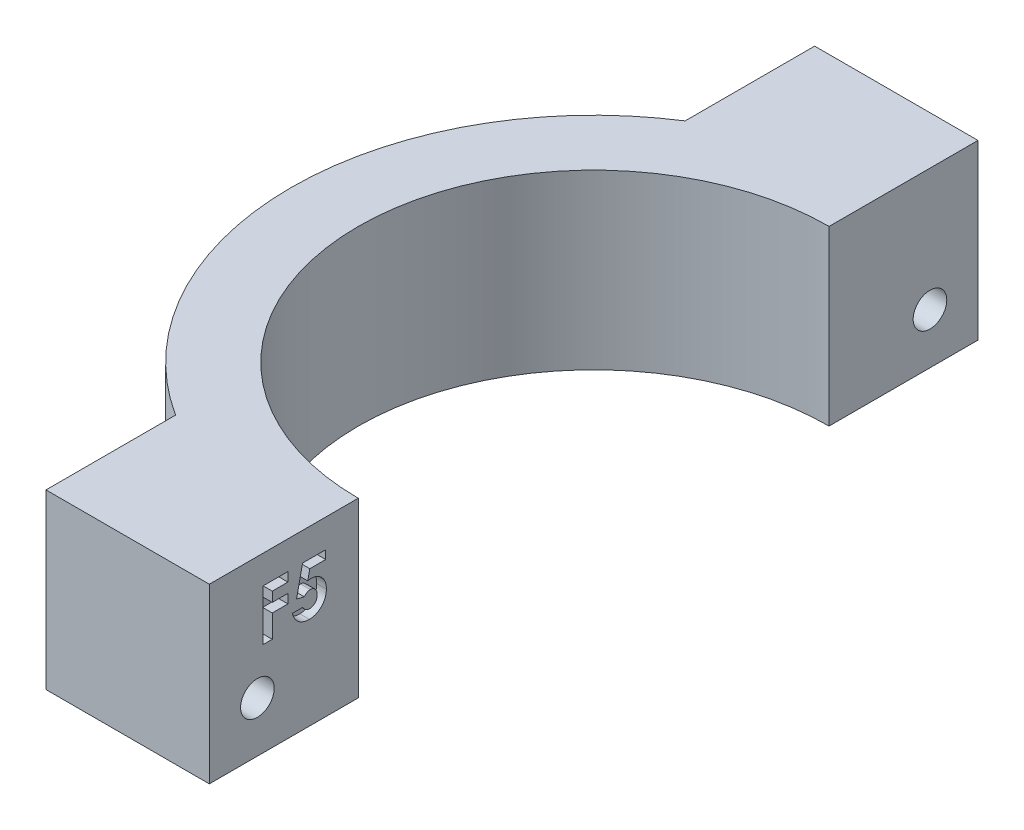
SolidWorks part; units mm, degrees
ref_plane "Front Plane" through (0, 0, 0) normal (0, 0, 1) x (1, 0, 0)
ref_plane "Top Plane" through (0, 0, 0) normal (0, 1, 0) x (1, 0, 0)
ref_plane "Right Plane" through (0, 0, 0) normal (1, 0, 0) x (0, 0, -1)
sketch "Sketch1" plane through (0, 0, 0) normal (0, 1, 0) x (1, 0, 0)
  line L0 (-46.9983, 32.5286) -> (-46.9983, -47.4714)
  line L1 (-46.9983, -47.4714) -> (-12.9983, -47.4714)
  line L2 (-12.9983, -47.4714) -> (-12.9983, -31.9714)
  line L3 (-46.9983, 32.5286) -> (-12.9983, 32.5286)
  line L4 (-12.9983, 32.5286) -> (-12.9983, 17.0286)
  line L5 (-29.9983, 32.5286) -> (-29.9983, 19.0474)
  line L6 (-29.9983, -47.4714) -> (-29.9983, -33.9903)
  arc A0 (-12.9983, 17.0286) -> (-12.9983, -31.9714) centre (-12.9983, -7.4714) ccw
  arc A1 (-12.9983, 24.0286) -> (-12.9983, -38.9714) centre (-12.9983, -7.4714) ccw
  dimension "D1" = 80
  dimension "D2" = 34
  dimension "D3" = 34
  dimension "D4" = 15.5
  dimension "D5" = 15.5
  dimension "D6" = 49
  dimension "D7" = 7
extrude "Boss-Extrude1" add sketch "Sketch1" along normal blind 18 contours A1 L4 L3 L5 | L4 A1 L2 A0 | A1 L6 L1 L2
sketch "Sketch2" plane through (-12.9983, 0, 0) normal (1, 0, 0) x (0, 0, -1)
  line L0 (-47.4714, 18) -> (-47.4714, 0) construction
  line L3 (32.5286, 18) -> (32.5286, 0) construction
  line L8 (-47.4714, 18) -> (-31.9714, 18) construction
  line L9 (32.5286, 18) -> (17.0286, 18) construction
  circle A0 centre (-42.4714, 5.25) radius 1.75
  circle A1 centre (27.5286, 5.25) radius 1.75
  dimension "D3" = 12.75
  dimension "D5" = 3.5
  dimension "D6" = 3.5
  dimension "D1" = 5
  dimension "D2" = 5
  dimension "D4" = 12.75
extrude "Cut-Extrude1" cut sketch "Sketch2" against normal through all
sketch "Sketch3" plane through (-12.9983, 0, 0) normal (1, 0, 0) x (0, 0, -1)
  text T0 "<b>F5</b>" font "Century Gothic" height in points 20
extrude "Cut-Extrude2" cut sketch "Sketch3" against normal blind 1
sketch "Sketch4" plane through (-29.9983, 0, 0) normal (-1, 0, 0) x (0, 0, 1)
  line L1 (-25.6511, 2.6891) -> (-24.372, 5.5955)
  line L2 (-24.372, 5.5955) -> (-26.2495, 8.1564)
  line L3 (-26.2495, 8.1564) -> (-29.406, 7.8109)
  line L4 (-29.406, 7.8109) -> (-30.6851, 4.9045)
  line L5 (-30.6851, 4.9045) -> (-28.8077, 2.3436)
  line L6 (-28.8077, 2.3436) -> (-25.6511, 2.6891)
  line L7 (44.0484, 2.4938) -> (45.6468, 5.2376)
  line L8 (45.6468, 5.2376) -> (44.0699, 7.9938)
  line L9 (44.0699, 7.9938) -> (40.8945, 8.0062)
  line L10 (40.8945, 8.0062) -> (39.296, 5.2624)
  line L11 (39.296, 5.2624) -> (40.873, 2.5062)
  line L12 (40.873, 2.5062) -> (44.0484, 2.4938)
  circle A0 centre (-27.5286, 5.25) radius 2.75 construction
  circle A1 centre (42.4714, 5.25) radius 2.75 construction
extrude "Cut-Extrude3" cut sketch "Sketch4" against normal blind 5
